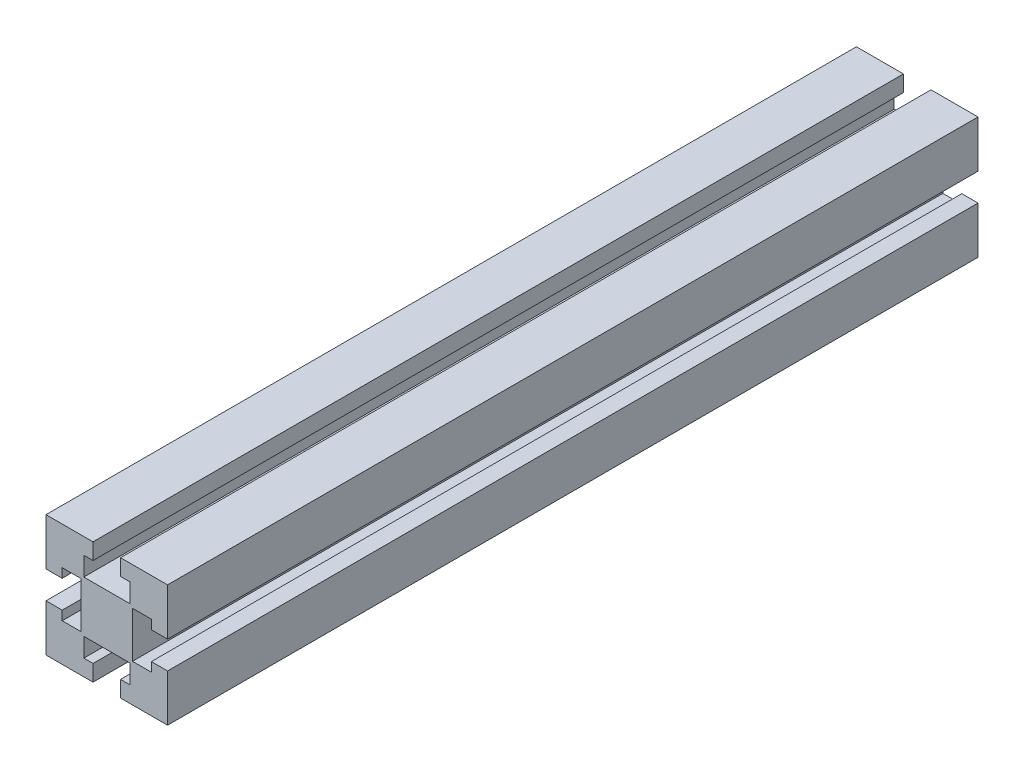
SolidWorks part; units mm, degrees
ref_plane "Ebene vorne" through (0, 0, 0) normal (0, 0, 1) x (1, 0, 0)
ref_plane "Ebene oben" through (0, 0, 0) normal (0, 1, 0) x (1, 0, 0)
ref_plane "Ebene rechts" through (0, 0, 0) normal (1, 0, 0) x (0, 0, -1)
sketch "Skizze1" plane through (0, 0, 0) normal (0, 0, 1) x (1, 0, 0)
  line L39 (-18.8192, 33.7768) -> (-1.4192, 33.7768)
  line L43 (-46.4192, 33.7768) -> (-29.0192, 33.7768)
  line L44 (-46.4192, 33.7768) -> (-46.4192, 16.3768)
  line L45 (-46.4192, -11.2232) -> (-29.0192, -11.2232)
  line L46 (-1.4192, 33.7768) -> (-1.4192, 16.3768)
  line L47 (-32.4242, 27.7768) -> (-29.0192, 27.7768)
  line L48 (-32.4242, 27.7768) -> (-32.4242, 20.7768)
  line L49 (-32.4242, 20.7768) -> (-15.4143, 20.7768)
  line L50 (-15.4143, 27.7768) -> (-15.4143, 20.7768)
  line L51 (-14.4192, 19.7817) -> (-7.4192, 19.7817)
  line L52 (-14.4192, 19.7817) -> (-14.4192, 2.7718)
  line L53 (-14.4192, 2.7718) -> (-7.4192, 2.7718)
  line L54 (-7.4192, 19.7817) -> (-7.4192, 16.3768)
  line L55 (-32.4242, 1.7768) -> (-15.4143, 1.7768)
  line L56 (-32.4242, 1.7768) -> (-32.4242, -5.2232)
  line L57 (-32.4242, -5.2232) -> (-29.0192, -5.2232)
  line L58 (-15.4143, 1.7768) -> (-15.4143, -5.2232)
  line L59 (-40.4192, 19.7817) -> (-33.4192, 19.7817)
  line L60 (-40.4192, 19.7817) -> (-40.4192, 16.3768)
  line L61 (-40.4192, 2.7718) -> (-33.4192, 2.7718)
  line L62 (-33.4192, 19.7817) -> (-33.4192, 2.7718)
  line L64 (-29.0192, 27.7768) -> (-29.0192, 33.7768)
  line L66 (-18.8192, 27.7768) -> (-18.8192, 33.7768)
  line L67 (-7.4192, 16.3768) -> (-1.4192, 16.3768)
  line L69 (-7.4192, 6.1768) -> (-1.4192, 6.1768)
  line L72 (-29.0192, -5.2232) -> (-29.0192, -11.2232)
  line L74 (-18.8192, -5.2232) -> (-18.8192, -11.2232)
  line L75 (-40.4192, 16.3768) -> (-46.4192, 16.3768)
  line L77 (-40.4192, 6.1768) -> (-46.4192, 6.1768)
  line L79 (-18.8192, 27.7768) -> (-15.4143, 27.7768)
  line L80 (-7.4192, 6.1768) -> (-7.4192, 2.7718)
  line L81 (-1.4192, 6.1768) -> (-1.4192, -11.2232)
  line L82 (-18.8192, -11.2232) -> (-1.4192, -11.2232)
  line L83 (-18.8192, -5.2232) -> (-15.4143, -5.2232)
  line L84 (-46.4192, 6.1768) -> (-46.4192, -11.2232)
  line L85 (-40.4192, 6.1768) -> (-40.4192, 2.7718)
  dimension "D6" = 13
  dimension "D4" = 13
  dimension "D1" = 10.2
  dimension "D2" = 45
  dimension "D3" = 45
  dimension "D5" = 13
  dimension "D7" = 13
  dimension "D8" = 6
  dimension "D9" = 13.995
extrude "Aufsatz-Linear austragen1" add sketch "Skizze1" along normal blind 300 contours L43 L64 L47 L48 L49 L50 L79 L66 L39 L46 L67 L54 L51 L52 L53 L80 L69 L81 L82 L74 L83 L58 L55 L56 L57 L72 L45 L84 L77 L85 L61 L62 L59 L60 L75 L44
